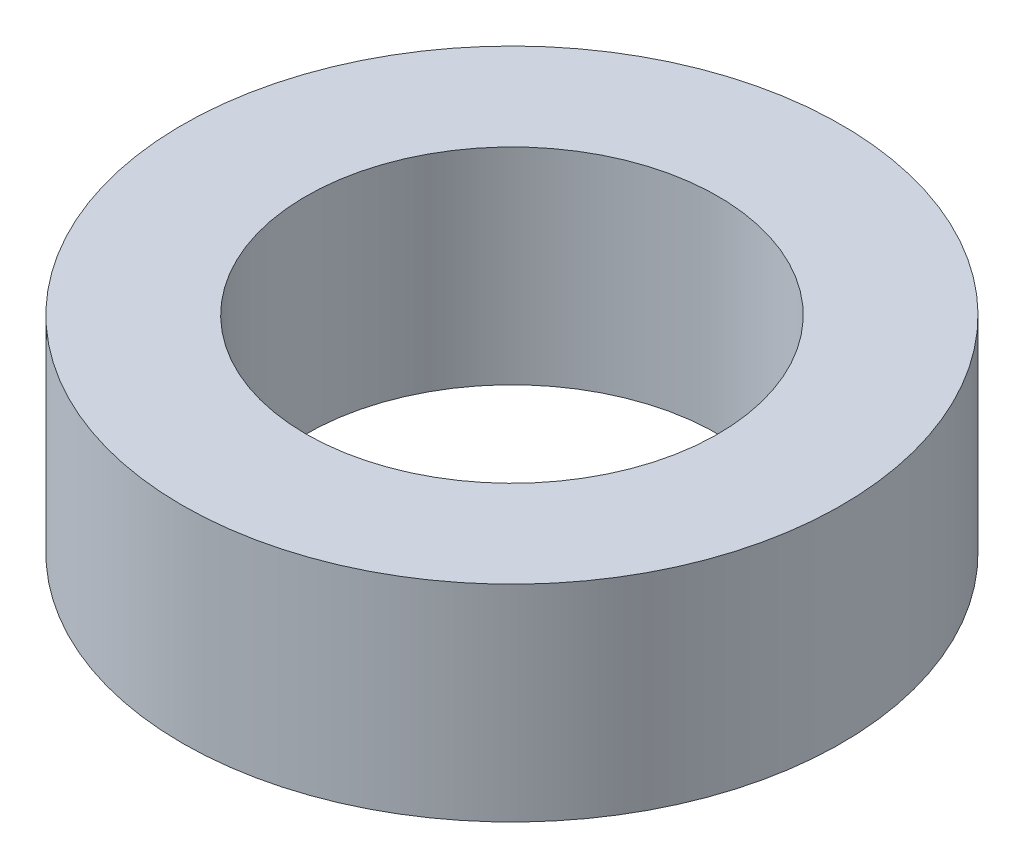
SolidWorks part; units mm, degrees
material "1023 Carbon Steel Sheet (SS)"
ref_plane "Front Plane" through (0, 0, 0) normal (0, 0, 1) x (1, 0, 0)
ref_plane "Top Plane" through (0, 0, 0) normal (0, 1, 0) x (1, 0, 0)
ref_plane "Right Plane" through (0, 0, 0) normal (1, 0, 0) x (0, 0, -1)
sketch "Sketch1" plane through (0, 0, 0) normal (0, 1, 0) x (1, 0, 0)
  circle A0 centre (0, 0) radius 4
  circle A1 centre (0, 0) radius 2.5
  dimension "D1" = 5
  dimension "D2" = 8
extrude "Boss-Extrude1" add sketch "Sketch1" along normal mid plane 2.5
